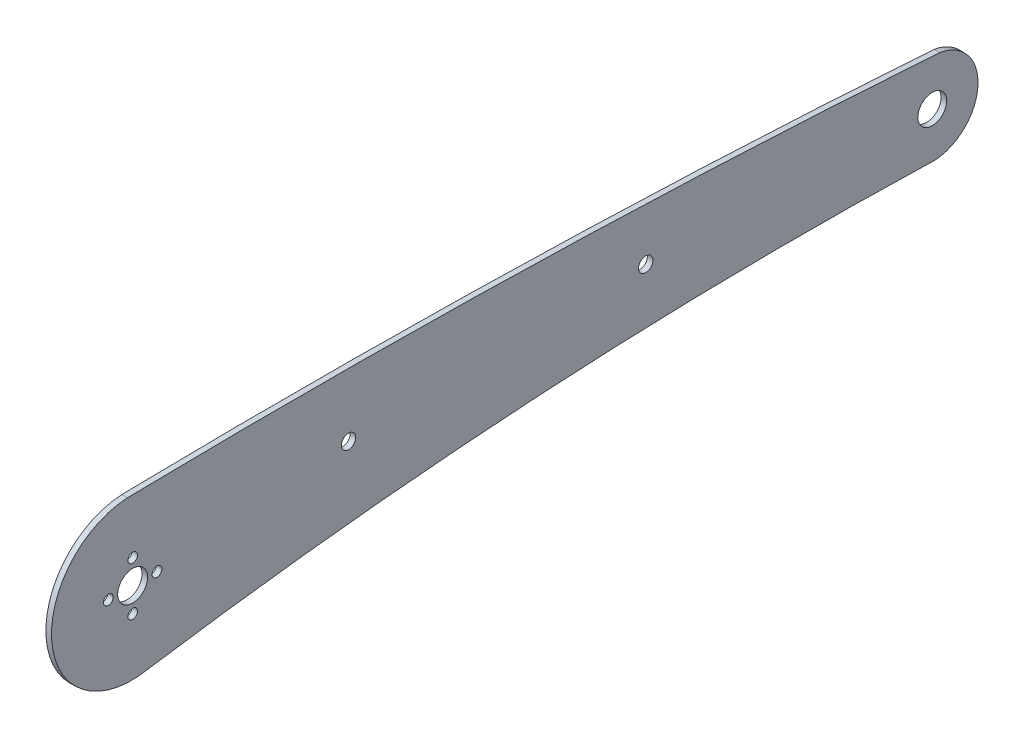
SolidWorks part; units mm, degrees
ref_plane "前基準面" through (0, 0, 0) normal (0, 0, 1) x (1, 0, 0)
ref_plane "上基準面" through (0, 0, 0) normal (0, 1, 0) x (1, 0, 0)
ref_plane "右基準面" through (0, 0, 0) normal (1, 0, 0) x (0, 0, -1)
sketch "草圖1" plane through (0, 0, 0) normal (1, 0, 0) x (0, 0, -1)
  circle A0 centre (-102.144, 6.6333) radius 1.3
  circle A1 centre (-108.644, 0.1333) radius 1.3
  circle A2 centre (-102.144, -6.3667) radius 1.3
  circle A3 centre (-95.644, 0.1333) radius 1.3
  circle A6 centre (-102.144, 0.1333) radius 4
  circle A8 centre (35.0011, 5.9829) radius 1.925
  circle A9 centre (-44.4328, 4.6867) radius 1.925
  arc A10 (111.556, -8.572) -> (-98.2301, -21.2449) centre (76.1692, -1165.5062) ccw
  arc A11 (-103.5418, 21.202) -> (-98.2301, -21.2449) centre (-102.3984, -0.2107) ccw
  arc A12 (111.556, -8.572) -> (112.407, -8.5887) centre (112.0794, -3.5995) ccw
  arc A13 (112.407, -8.5887) -> (113.5845, 15.6966) centre (111.6053, 3.6213) ccw
  arc A14 (113.5845, 15.6966) -> (-103.5418, 21.202) centre (-56.6324, -2413.0729) ccw
  circle A15 centre (111.6053, 3.6213) radius 3.85
extrude "填料-伸長1" add sketch "草圖1" along normal blind 1.5
